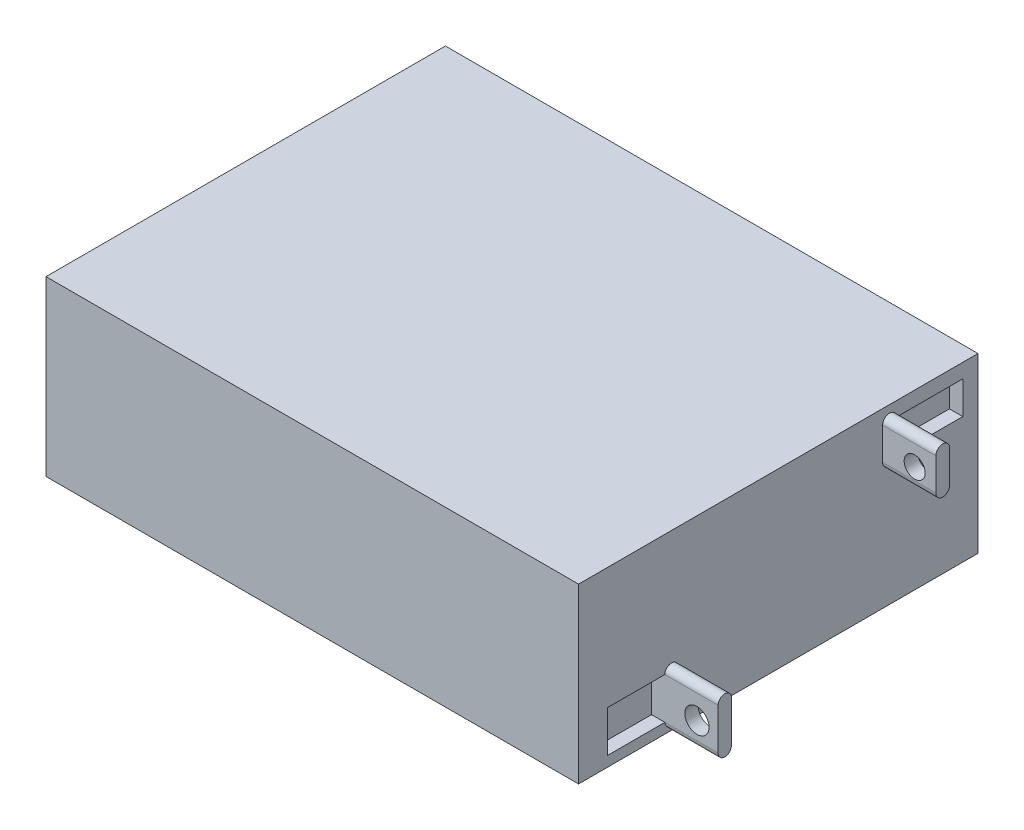
SolidWorks part; units mm, degrees
ref_plane "Front Plane" through (0, 0, 0) normal (0, 0, 1) x (1, 0, 0)
ref_plane "Top Plane" through (0, 0, 0) normal (0, 1, 0) x (1, 0, 0)
ref_plane "Right Plane" through (0, 0, 0) normal (1, 0, 0) x (0, 0, -1)
sketch "Sketch1" plane through (0, 0, 0) normal (0, 1, 0) x (1, 0, 0)
  line L1 (-26.1274, -34.2203) -> (75.4726, -34.2203)
  line L2 (-26.1274, -34.2203) -> (-26.1274, 41.9797)
  line L3 (-26.1274, 41.9797) -> (75.4726, 41.9797)
  line L4 (75.4726, -34.2203) -> (75.4726, 41.9797)
  dimension "D1" = 101.6
  dimension "D2" = 76.2
extrude "Boss-Extrude1" add sketch "Sketch1" along normal blind 33.02
sketch "Sketch2" plane through (75.4726, 0, 0) normal (1, 0, 0) x (0, 0, -1)
  line L0 (25.0912, 30.2947) -> (25.0912, 24.1463) construction
  line L1 (26.4028, 30.2947) -> (26.4028, 24.1463)
  line L2 (23.7795, 30.2947) -> (23.7795, 24.1463)
  line L3 (-16.4906, 9.8561) -> (-16.4906, 1.9548) construction
  line L4 (-15.2207, 9.8561) -> (-15.2207, 1.9548)
  line L5 (-17.7604, 9.8561) -> (-17.7604, 1.9548)
  arc A0 (26.4028, 30.2947) -> (23.7795, 30.2947) centre (25.0912, 30.2947) ccw
  arc A1 (23.7795, 24.1463) -> (26.4028, 24.1463) centre (25.0912, 24.1463) ccw
  arc A2 (-15.2207, 9.8561) -> (-17.7604, 9.8561) centre (-16.4906, 9.8561) ccw
  arc A3 (-17.7604, 1.9548) -> (-15.2207, 1.9548) centre (-16.4906, 1.9548) ccw
  point P2 (25.0912, 27.2205)
  point P7 (-16.4906, 5.9055)
extrude "Boss-Extrude2" add sketch "Sketch2" along normal blind 10.16
sketch "Sketch3" plane through (0, 0, -26.4028) normal (0, 0, -1) x (-1, 0, 0)
  circle A0 centre (-81.5935, 26.4377) radius 2.0071
  circle A1 centre (-81.5935, 5.3361) radius 2.3097
extrude "Cut-Extrude1" cut sketch "Sketch3" against normal blind 58.42
sketch "Sketch4" plane through (75.4726, 0, 0) normal (1, 0, 0) x (0, 0, -1)
  line L1 (26.4028, 30.2947) -> (39.0724, 30.2947)
  line L2 (26.4028, 30.2947) -> (26.4028, 24.0576)
  line L3 (26.4028, 24.0576) -> (39.0724, 24.0576)
  line L4 (39.0724, 30.2947) -> (39.0724, 24.0576)
extrude "Cut-Extrude2" cut sketch "Sketch4" against normal blind 2.54
sketch "Sketch5" plane through (75.4726, 0, 0) normal (1, 0, 0) x (0, 0, -1)
  line L1 (-17.7604, 9.8561) -> (-28.7265, 9.8561)
  line L2 (-17.7604, 9.8561) -> (-17.7604, 1.9548)
  line L3 (-17.7604, 1.9548) -> (-28.7265, 1.9548)
  line L4 (-28.7265, 9.8561) -> (-28.7265, 1.9548)
extrude "Cut-Extrude3" cut sketch "Sketch5" against normal blind 2.54
sketch "Sketch7" plane through (0, 0, 34.2203) normal (0, 0, 1) x (1, 0, 0)
  text T0 "REACHAREABLE SEALED LEAD-ACID BATTERY\r\n                       6V 4.5Ah" font "Century Gothic" height 3.5
sketch "Sketch8" plane through (0, 0, -41.9797) normal (0, 0, -1) x (-1, 0, 0)
  text T0 "RECHARGEABLE SEAL LEAD-ACID \r\n BATTERY 6V 4.5Ah" font "Century Gothic" height 3.5
extrude "Boss-Extrude3" add sketch "Sketch8" along normal blind 0.254
